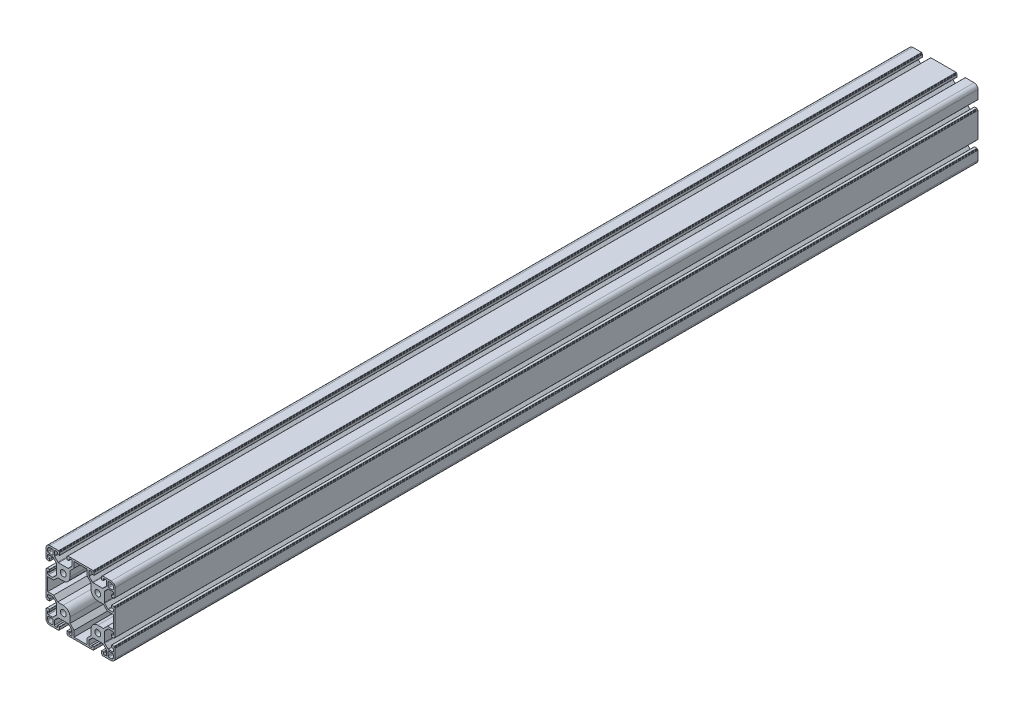
SolidWorks part; units mm, degrees
material "6063 T5"
ref_plane "Спереди" through (0, 0, 0) normal (0, 0, 1) x (1, 0, 0)
ref_plane "Сверху" through (0, 0, 0) normal (0, 1, 0) x (1, 0, 0)
ref_plane "Справа" through (0, 0, 0) normal (1, 0, 0) x (0, 0, -1)
sketch "Эскиз1" plane through (0, 0, 0) normal (0, 0, 1) x (1, 0, 0)
  line L0 (-19.98, 20.5457) -> (20.02, 20.5457) construction
  line L1 (-20, 10.25) -> (-20, 15.5)
  line L2 (-15.5, 20) -> (-10.25, 20)
  line L3 (20, 0) -> (20, -40) construction
  line L4 (-12.8, 11.8) -> (-17, 11.8)
  line L5 (-11.8, 12.8) -> (-11.8, 17)
  line L6 (-12.8, 18) -> (-15.5, 18)
  line L7 (-18, 12.8) -> (-18, 15.5)
  line L8 (0, 0) -> (40, 0) construction
  line L13 (0, 0) -> (0, -40) construction
  line L14 (0, -40) -> (40, -40) construction
  line L19 (40, 0) -> (40, -40) construction
  line L20 (50.25, 20) -> (55.5, 20)
  line L25 (0, -20) -> (40, -20) construction
  line L26 (60, 15.5) -> (60, 10.25)
  line L27 (51.8, 12.8) -> (51.8, 17)
  line L28 (52.8, 11.8) -> (57, 11.8)
  line L29 (58, 12.8) -> (58, 15.5)
  line L30 (52.8, 18) -> (55.5, 18)
  line L31 (60, -50.25) -> (60, -55.5)
  line L32 (55.5, -60) -> (50.25, -60)
  line L33 (52.8, -51.8) -> (57, -51.8)
  line L34 (51.8, -52.8) -> (51.8, -57)
  line L35 (52.8, -58) -> (55.5, -58)
  line L36 (58, -52.8) -> (58, -55.5)
  line L37 (-10.25, -60) -> (-15.5, -60)
  line L38 (-20, -55.5) -> (-20, -50.25)
  line L39 (-11.8, -52.8) -> (-11.8, -57)
  line L40 (-12.8, -51.8) -> (-17, -51.8)
  line L41 (-18, -52.8) -> (-18, -55.5)
  line L42 (-12.8, -58) -> (-15.5, -58)
  line L43 (10.25, 20) -> (29.75, 20)
  line L44 (60, -10.25) -> (60, -29.75)
  line L45 (29.75, -60) -> (10.25, -60)
  line L46 (-20, -29.75) -> (-20, -10.25)
  line L47 (-20.044, 23.5406) -> (59.956, 23.5406) construction
  line L48 (-18, -27.55) -> (-18, -12.45)
  line L49 (-18, -12.45) -> (-11.1387, -12.45)
  line L50 (-11.1387, -12.45) -> (-6.4887, -7.8)
  line L51 (-6.4887, -7.8) -> (0, -7.8)
  line L52 (7.8, 0) -> (7.8, 6.4887)
  line L53 (7.8, 6.4887) -> (12.45, 11.1387)
  line L54 (12.45, 11.1387) -> (12.45, 18)
  line L55 (12.45, 18) -> (27.55, 18)
  line L56 (12.45, -58) -> (27.55, -58)
  line L57 (12.45, -51.1387) -> (12.45, -58)
  line L58 (7.8, -46.4887) -> (12.45, -51.1387)
  line L59 (7.8, -40) -> (7.8, -46.4887)
  line L60 (-6.4887, -32.2) -> (0, -32.2)
  line L61 (-11.1387, -27.55) -> (-6.4887, -32.2)
  line L62 (-18, -27.55) -> (-11.1387, -27.55)
  line L63 (27.55, -51.1387) -> (27.55, -58)
  line L64 (32.2, -46.4887) -> (27.55, -51.1387)
  line L65 (32.2, -40) -> (32.2, -46.4887)
  line L66 (46.4887, -32.2) -> (40, -32.2)
  line L67 (51.1387, -27.55) -> (46.4887, -32.2)
  line L68 (58, -27.55) -> (51.1387, -27.55)
  line L69 (58, -27.55) -> (58, -12.45)
  line L70 (58, -12.45) -> (51.1387, -12.45)
  line L71 (51.1387, -12.45) -> (46.4887, -7.8)
  line L72 (46.4887, -7.8) -> (40, -7.8)
  line L73 (32.2, 0) -> (32.2, 6.4887)
  line L74 (32.2, 6.4887) -> (27.55, 11.1387)
  line L75 (27.55, 11.1387) -> (27.55, 18)
  arc A0 (-20, 15.5) -> (-15.5, 20) centre (-15.5, 15.5) cw
  arc A1 (-15.5, 18) -> (-18, 15.5) centre (-15.5, 15.5) ccw
  arc A2 (-17, 11.8) -> (-18, 12.8) centre (-17, 12.8) cw
  arc A3 (-12.8, 11.8) -> (-11.8, 12.8) centre (-12.8, 12.8) ccw
  arc A4 (-11.8, 17) -> (-12.8, 18) centre (-12.8, 17) ccw
  circle A5 centre (0, 0) radius 3.4
  arc A6 (55.5, 20) -> (60, 15.5) centre (55.5, 15.5) cw
  arc A11 (58, 15.5) -> (55.5, 18) centre (55.5, 15.5) ccw
  arc A16 (51.8, 17) -> (52.8, 18) centre (52.8, 17) cw
  arc A21 (51.8, 12.8) -> (52.8, 11.8) centre (52.8, 12.8) ccw
  arc A22 (57, 11.8) -> (58, 12.8) centre (57, 12.8) ccw
  circle A23 centre (40, 0) radius 3.4
  arc A24 (60, -55.5) -> (55.5, -60) centre (55.5, -55.5) cw
  arc A25 (55.5, -58) -> (58, -55.5) centre (55.5, -55.5) ccw
  arc A26 (57, -51.8) -> (58, -52.8) centre (57, -52.8) cw
  arc A27 (52.8, -51.8) -> (51.8, -52.8) centre (52.8, -52.8) ccw
  arc A28 (51.8, -57) -> (52.8, -58) centre (52.8, -57) ccw
  circle A29 centre (40, -40) radius 3.4
  arc A30 (-15.5, -60) -> (-20, -55.5) centre (-15.5, -55.5) cw
  arc A31 (-18, -55.5) -> (-15.5, -58) centre (-15.5, -55.5) ccw
  arc A32 (-11.8, -57) -> (-12.8, -58) centre (-12.8, -57) cw
  arc A33 (-11.8, -52.8) -> (-12.8, -51.8) centre (-12.8, -52.8) ccw
  arc A34 (-17, -51.8) -> (-18, -52.8) centre (-17, -52.8) ccw
  circle A35 centre (0, -40) radius 3.4
  arc A36 (0, -7.8) -> (7.8, 0) centre (0, 0) ccw
  arc A37 (0, -32.2) -> (7.8, -40) centre (0, -40) cw
  arc A38 (40, -32.2) -> (32.2, -40) centre (40, -40) ccw
  arc A39 (40, -7.8) -> (32.2, 0) centre (40, 0) cw
  point P5 (0, 0)
  point P27 (20, -20)
  point P36 (40, 0)
  point P57 (40, -40)
  point P77 (0, -40)
  point P94 (20, -20)
  point P122 (-18, -20)
  point P127 (20, -58)
  point P138 (20, 18)
  line B0 (-20, 10.25) -> (-20, 5.4)
  line B1 (-19.7, 5.1) -> (-19.3, 5.1)
  line B2 (-19, 4.8) -> (-19, 4.4)
  line B3 (-18.7, 4.1) -> (-16, 4.1)
  line B4 (-15.7, 4.4) -> (-15.7, 6.3)
  line B5 (-16, 6.6) -> (-17.2, 6.6)
  line B6 (-18.2, 7.6) -> (-18.2, 9.25)
  line B7 (-17.2, 10.25) -> (-12.4642, 10.25)
  line B8 (-11.7571, 9.9571) -> (-7.9929, 6.1929)
  line B9 (-7.7, 5.4858) -> (-7.7, -5.4858)
  line B10 (-7.7, 0) -> (-20, 0) construction
  line B11 (-11.7571, -9.9571) -> (-7.9929, -6.1929)
  line B12 (-17.2, -10.25) -> (-12.4642, -10.25)
  line B13 (-18.2, -7.6) -> (-18.2, -9.25)
  line B14 (-16, -6.6) -> (-17.2, -6.6)
  line B15 (-15.7, -4.4) -> (-15.7, -6.3)
  line B16 (-18.7, -4.1) -> (-16, -4.1)
  line B17 (-19, -4.8) -> (-19, -4.4)
  line B18 (-19.7, -5.1) -> (-19.3, -5.1)
  line B19 (-20, -10.25) -> (-20, -5.4)
  arc B20 (-15.7, 6.3) -> (-16, 6.6) centre (-16, 6.3) ccw
  arc B21 (-16, 4.1) -> (-15.7, 4.4) centre (-16, 4.4) ccw
  arc B22 (-19, 4.4) -> (-18.7, 4.1) centre (-18.7, 4.4) ccw
  arc B23 (-19.3, 5.1) -> (-19, 4.8) centre (-19.3, 4.8) cw
  arc B24 (-20, 5.4) -> (-19.7, 5.1) centre (-19.7, 5.4) ccw
  arc B25 (-7.9929, 6.1929) -> (-7.7, 5.4858) centre (-8.7, 5.4858) cw
  arc B26 (-12.4642, 10.25) -> (-11.7571, 9.9571) centre (-12.4642, 9.25) cw
  arc B27 (-18.2, 9.25) -> (-17.2, 10.25) centre (-17.2, 9.25) cw
  arc B28 (-17.2, 6.6) -> (-18.2, 7.6) centre (-17.2, 7.6) cw
  arc B29 (-17.2, -6.6) -> (-18.2, -7.6) centre (-17.2, -7.6) ccw
  arc B30 (-18.2, -9.25) -> (-17.2, -10.25) centre (-17.2, -9.25) ccw
  arc B31 (-12.4642, -10.25) -> (-11.7571, -9.9571) centre (-12.4642, -9.25) ccw
  arc B32 (-7.9929, -6.1929) -> (-7.7, -5.4858) centre (-8.7, -5.4858) ccw
  arc B33 (-20, -5.4) -> (-19.7, -5.1) centre (-19.7, -5.4) cw
  arc B34 (-19.3, -5.1) -> (-19, -4.8) centre (-19.3, -4.8) ccw
  arc B35 (-19, -4.4) -> (-18.7, -4.1) centre (-18.7, -4.4) cw
  arc B36 (-16, -4.1) -> (-15.7, -4.4) centre (-16, -4.4) cw
  arc B37 (-15.7, -6.3) -> (-16, -6.6) centre (-16, -6.3) cw
  line B38 (10.25, 20) -> (5.4, 20)
  line B39 (5.1, 19.7) -> (5.1, 19.3)
  line B40 (4.8, 19) -> (4.4, 19)
  line B41 (4.1, 18.7) -> (4.1, 16)
  line B42 (4.4, 15.7) -> (6.3, 15.7)
  line B43 (6.6, 16) -> (6.6, 17.2)
  line B44 (7.6, 18.2) -> (9.25, 18.2)
  line B45 (10.25, 17.2) -> (10.25, 12.4642)
  line B46 (9.9571, 11.7571) -> (6.1929, 7.9929)
  line B47 (5.4858, 7.7) -> (-5.4858, 7.7)
  line B48 (0, 7.7) -> (0, 20) construction
  line B49 (-9.9571, 11.7571) -> (-6.1929, 7.9929)
  line B50 (-10.25, 17.2) -> (-10.25, 12.4642)
  line B51 (-7.6, 18.2) -> (-9.25, 18.2)
  line B52 (-6.6, 16) -> (-6.6, 17.2)
  line B53 (-4.4, 15.7) -> (-6.3, 15.7)
  line B54 (-4.1, 18.7) -> (-4.1, 16)
  line B55 (-4.8, 19) -> (-4.4, 19)
  line B56 (-5.1, 19.7) -> (-5.1, 19.3)
  line B57 (-10.25, 20) -> (-5.4, 20)
  arc B58 (6.3, 15.7) -> (6.6, 16) centre (6.3, 16) ccw
  arc B59 (4.1, 16) -> (4.4, 15.7) centre (4.4, 16) ccw
  arc B60 (4.4, 19) -> (4.1, 18.7) centre (4.4, 18.7) ccw
  arc B61 (5.1, 19.3) -> (4.8, 19) centre (4.8, 19.3) cw
  arc B62 (5.4, 20) -> (5.1, 19.7) centre (5.4, 19.7) ccw
  arc B63 (6.1929, 7.9929) -> (5.4858, 7.7) centre (5.4858, 8.7) cw
  arc B64 (10.25, 12.4642) -> (9.9571, 11.7571) centre (9.25, 12.4642) cw
  arc B65 (9.25, 18.2) -> (10.25, 17.2) centre (9.25, 17.2) cw
  arc B66 (6.6, 17.2) -> (7.6, 18.2) centre (7.6, 17.2) cw
  arc B67 (-6.6, 17.2) -> (-7.6, 18.2) centre (-7.6, 17.2) ccw
  arc B68 (-9.25, 18.2) -> (-10.25, 17.2) centre (-9.25, 17.2) ccw
  arc B69 (-10.25, 12.4642) -> (-9.9571, 11.7571) centre (-9.25, 12.4642) ccw
  arc B70 (-6.1929, 7.9929) -> (-5.4858, 7.7) centre (-5.4858, 8.7) ccw
  arc B71 (-5.4, 20) -> (-5.1, 19.7) centre (-5.4, 19.7) cw
  arc B72 (-5.1, 19.3) -> (-4.8, 19) centre (-4.8, 19.3) ccw
  arc B73 (-4.4, 19) -> (-4.1, 18.7) centre (-4.4, 18.7) cw
  arc B74 (-4.1, 16) -> (-4.4, 15.7) centre (-4.4, 16) cw
  arc B75 (-6.3, 15.7) -> (-6.6, 16) centre (-6.3, 16) cw
  line B76 (50.25, 20) -> (45.4, 20)
  line B77 (45.1, 19.7) -> (45.1, 19.3)
  line B78 (44.8, 19) -> (44.4, 19)
  line B79 (44.1, 18.7) -> (44.1, 16)
  line B80 (44.4, 15.7) -> (46.3, 15.7)
  line B81 (46.6, 16) -> (46.6, 17.2)
  line B82 (47.6, 18.2) -> (49.25, 18.2)
  line B83 (50.25, 17.2) -> (50.25, 12.4642)
  line B84 (49.9571, 11.7571) -> (46.1929, 7.9929)
  line B85 (45.4858, 7.7) -> (34.5142, 7.7)
  line B86 (40, 7.7) -> (40, 20) construction
  line B87 (30.0429, 11.7571) -> (33.8071, 7.9929)
  line B88 (29.75, 17.2) -> (29.75, 12.4642)
  line B89 (32.4, 18.2) -> (30.75, 18.2)
  line B90 (33.4, 16) -> (33.4, 17.2)
  line B91 (35.6, 15.7) -> (33.7, 15.7)
  line B92 (35.9, 18.7) -> (35.9, 16)
  line B93 (35.2, 19) -> (35.6, 19)
  line B94 (34.9, 19.7) -> (34.9, 19.3)
  line B95 (29.75, 20) -> (34.6, 20)
  arc B96 (46.3, 15.7) -> (46.6, 16) centre (46.3, 16) ccw
  arc B97 (44.1, 16) -> (44.4, 15.7) centre (44.4, 16) ccw
  arc B98 (44.4, 19) -> (44.1, 18.7) centre (44.4, 18.7) ccw
  arc B99 (45.1, 19.3) -> (44.8, 19) centre (44.8, 19.3) cw
  arc B100 (45.4, 20) -> (45.1, 19.7) centre (45.4, 19.7) ccw
  arc B101 (46.1929, 7.9929) -> (45.4858, 7.7) centre (45.4858, 8.7) cw
  arc B102 (50.25, 12.4642) -> (49.9571, 11.7571) centre (49.25, 12.4642) cw
  arc B103 (49.25, 18.2) -> (50.25, 17.2) centre (49.25, 17.2) cw
  arc B104 (46.6, 17.2) -> (47.6, 18.2) centre (47.6, 17.2) cw
  arc B105 (33.4, 17.2) -> (32.4, 18.2) centre (32.4, 17.2) ccw
  arc B106 (30.75, 18.2) -> (29.75, 17.2) centre (30.75, 17.2) ccw
  arc B107 (29.75, 12.4642) -> (30.0429, 11.7571) centre (30.75, 12.4642) ccw
  arc B108 (33.8071, 7.9929) -> (34.5142, 7.7) centre (34.5142, 8.7) ccw
  arc B109 (34.6, 20) -> (34.9, 19.7) centre (34.6, 19.7) cw
  arc B110 (34.9, 19.3) -> (35.2, 19) centre (35.2, 19.3) ccw
  arc B111 (35.6, 19) -> (35.9, 18.7) centre (35.6, 18.7) cw
  arc B112 (35.9, 16) -> (35.6, 15.7) centre (35.6, 16) cw
  arc B113 (33.7, 15.7) -> (33.4, 16) centre (33.7, 16) cw
  line B114 (60, -10.25) -> (60, -5.4)
  line B115 (59.7, -5.1) -> (59.3, -5.1)
  line B116 (59, -4.8) -> (59, -4.4)
  line B117 (58.7, -4.1) -> (56, -4.1)
  line B118 (55.7, -4.4) -> (55.7, -6.3)
  line B119 (56, -6.6) -> (57.2, -6.6)
  line B120 (58.2, -7.6) -> (58.2, -9.25)
  line B121 (57.2, -10.25) -> (52.4642, -10.25)
  line B122 (51.7571, -9.9571) -> (47.9929, -6.1929)
  line B123 (47.7, -5.4858) -> (47.7, 5.4858)
  line B124 (47.7, 0) -> (60, 0) construction
  line B125 (51.7571, 9.9571) -> (47.9929, 6.1929)
  line B126 (57.2, 10.25) -> (52.4642, 10.25)
  line B127 (58.2, 7.6) -> (58.2, 9.25)
  line B128 (56, 6.6) -> (57.2, 6.6)
  line B129 (55.7, 4.4) -> (55.7, 6.3)
  line B130 (58.7, 4.1) -> (56, 4.1)
  line B131 (59, 4.8) -> (59, 4.4)
  line B132 (59.7, 5.1) -> (59.3, 5.1)
  line B133 (60, 10.25) -> (60, 5.4)
  arc B134 (55.7, -6.3) -> (56, -6.6) centre (56, -6.3) ccw
  arc B135 (56, -4.1) -> (55.7, -4.4) centre (56, -4.4) ccw
  arc B136 (59, -4.4) -> (58.7, -4.1) centre (58.7, -4.4) ccw
  arc B137 (59.3, -5.1) -> (59, -4.8) centre (59.3, -4.8) cw
  arc B138 (60, -5.4) -> (59.7, -5.1) centre (59.7, -5.4) ccw
  arc B139 (47.9929, -6.1929) -> (47.7, -5.4858) centre (48.7, -5.4858) cw
  arc B140 (52.4642, -10.25) -> (51.7571, -9.9571) centre (52.4642, -9.25) cw
  arc B141 (58.2, -9.25) -> (57.2, -10.25) centre (57.2, -9.25) cw
  arc B142 (57.2, -6.6) -> (58.2, -7.6) centre (57.2, -7.6) cw
  arc B143 (57.2, 6.6) -> (58.2, 7.6) centre (57.2, 7.6) ccw
  arc B144 (58.2, 9.25) -> (57.2, 10.25) centre (57.2, 9.25) ccw
  arc B145 (52.4642, 10.25) -> (51.7571, 9.9571) centre (52.4642, 9.25) ccw
  arc B146 (47.9929, 6.1929) -> (47.7, 5.4858) centre (48.7, 5.4858) ccw
  arc B147 (60, 5.4) -> (59.7, 5.1) centre (59.7, 5.4) cw
  arc B148 (59.3, 5.1) -> (59, 4.8) centre (59.3, 4.8) ccw
  arc B149 (59, 4.4) -> (58.7, 4.1) centre (58.7, 4.4) cw
  arc B150 (56, 4.1) -> (55.7, 4.4) centre (56, 4.4) cw
  arc B151 (55.7, 6.3) -> (56, 6.6) centre (56, 6.3) cw
  line B152 (60, -50.25) -> (60, -45.4)
  line B153 (59.7, -45.1) -> (59.3, -45.1)
  line B154 (59, -44.8) -> (59, -44.4)
  line B155 (58.7, -44.1) -> (56, -44.1)
  line B156 (55.7, -44.4) -> (55.7, -46.3)
  line B157 (56, -46.6) -> (57.2, -46.6)
  line B158 (58.2, -47.6) -> (58.2, -49.25)
  line B159 (57.2, -50.25) -> (52.4642, -50.25)
  line B160 (51.7571, -49.9571) -> (47.9929, -46.1929)
  line B161 (47.7, -45.4858) -> (47.7, -34.5142)
  line B162 (47.7, -40) -> (60, -40) construction
  line B163 (51.7571, -30.0429) -> (47.9929, -33.8071)
  line B164 (57.2, -29.75) -> (52.4642, -29.75)
  line B165 (58.2, -32.4) -> (58.2, -30.75)
  line B166 (56, -33.4) -> (57.2, -33.4)
  line B167 (55.7, -35.6) -> (55.7, -33.7)
  line B168 (58.7, -35.9) -> (56, -35.9)
  line B169 (59, -35.2) -> (59, -35.6)
  line B170 (59.7, -34.9) -> (59.3, -34.9)
  line B171 (60, -29.75) -> (60, -34.6)
  arc B172 (55.7, -46.3) -> (56, -46.6) centre (56, -46.3) ccw
  arc B173 (56, -44.1) -> (55.7, -44.4) centre (56, -44.4) ccw
  arc B174 (59, -44.4) -> (58.7, -44.1) centre (58.7, -44.4) ccw
  arc B175 (59.3, -45.1) -> (59, -44.8) centre (59.3, -44.8) cw
  arc B176 (60, -45.4) -> (59.7, -45.1) centre (59.7, -45.4) ccw
  arc B177 (47.9929, -46.1929) -> (47.7, -45.4858) centre (48.7, -45.4858) cw
  arc B178 (52.4642, -50.25) -> (51.7571, -49.9571) centre (52.4642, -49.25) cw
  arc B179 (58.2, -49.25) -> (57.2, -50.25) centre (57.2, -49.25) cw
  arc B180 (57.2, -46.6) -> (58.2, -47.6) centre (57.2, -47.6) cw
  arc B181 (57.2, -33.4) -> (58.2, -32.4) centre (57.2, -32.4) ccw
  arc B182 (58.2, -30.75) -> (57.2, -29.75) centre (57.2, -30.75) ccw
  arc B183 (52.4642, -29.75) -> (51.7571, -30.0429) centre (52.4642, -30.75) ccw
  arc B184 (47.9929, -33.8071) -> (47.7, -34.5142) centre (48.7, -34.5142) ccw
  arc B185 (60, -34.6) -> (59.7, -34.9) centre (59.7, -34.6) cw
  arc B186 (59.3, -34.9) -> (59, -35.2) centre (59.3, -35.2) ccw
  arc B187 (59, -35.6) -> (58.7, -35.9) centre (58.7, -35.6) cw
  arc B188 (56, -35.9) -> (55.7, -35.6) centre (56, -35.6) cw
  arc B189 (55.7, -33.7) -> (56, -33.4) centre (56, -33.7) cw
  line B190 (29.75, -60) -> (34.6, -60)
  line B191 (34.9, -59.7) -> (34.9, -59.3)
  line B192 (35.2, -59) -> (35.6, -59)
  line B193 (35.9, -58.7) -> (35.9, -56)
  line B194 (35.6, -55.7) -> (33.7, -55.7)
  line B195 (33.4, -56) -> (33.4, -57.2)
  line B196 (32.4, -58.2) -> (30.75, -58.2)
  line B197 (29.75, -57.2) -> (29.75, -52.4642)
  line B198 (30.0429, -51.7571) -> (33.8071, -47.9929)
  line B199 (34.5142, -47.7) -> (45.4858, -47.7)
  line B200 (40, -47.7) -> (40, -60) construction
  line B201 (49.9571, -51.7571) -> (46.1929, -47.9929)
  line B202 (50.25, -57.2) -> (50.25, -52.4642)
  line B203 (47.6, -58.2) -> (49.25, -58.2)
  line B204 (46.6, -56) -> (46.6, -57.2)
  line B205 (44.4, -55.7) -> (46.3, -55.7)
  line B206 (44.1, -58.7) -> (44.1, -56)
  line B207 (44.8, -59) -> (44.4, -59)
  line B208 (45.1, -59.7) -> (45.1, -59.3)
  line B209 (50.25, -60) -> (45.4, -60)
  arc B210 (33.7, -55.7) -> (33.4, -56) centre (33.7, -56) ccw
  arc B211 (35.9, -56) -> (35.6, -55.7) centre (35.6, -56) ccw
  arc B212 (35.6, -59) -> (35.9, -58.7) centre (35.6, -58.7) ccw
  arc B213 (34.9, -59.3) -> (35.2, -59) centre (35.2, -59.3) cw
  arc B214 (34.6, -60) -> (34.9, -59.7) centre (34.6, -59.7) ccw
  arc B215 (33.8071, -47.9929) -> (34.5142, -47.7) centre (34.5142, -48.7) cw
  arc B216 (29.75, -52.4642) -> (30.0429, -51.7571) centre (30.75, -52.4642) cw
  arc B217 (30.75, -58.2) -> (29.75, -57.2) centre (30.75, -57.2) cw
  arc B218 (33.4, -57.2) -> (32.4, -58.2) centre (32.4, -57.2) cw
  arc B219 (46.6, -57.2) -> (47.6, -58.2) centre (47.6, -57.2) ccw
  arc B220 (49.25, -58.2) -> (50.25, -57.2) centre (49.25, -57.2) ccw
  arc B221 (50.25, -52.4642) -> (49.9571, -51.7571) centre (49.25, -52.4642) ccw
  arc B222 (46.1929, -47.9929) -> (45.4858, -47.7) centre (45.4858, -48.7) ccw
  arc B223 (45.4, -60) -> (45.1, -59.7) centre (45.4, -59.7) cw
  arc B224 (45.1, -59.3) -> (44.8, -59) centre (44.8, -59.3) ccw
  arc B225 (44.4, -59) -> (44.1, -58.7) centre (44.4, -58.7) cw
  arc B226 (44.1, -56) -> (44.4, -55.7) centre (44.4, -56) cw
  arc B227 (46.3, -55.7) -> (46.6, -56) centre (46.3, -56) cw
  line B228 (-10.25, -60) -> (-5.4, -60)
  line B229 (-5.1, -59.7) -> (-5.1, -59.3)
  line B230 (-4.8, -59) -> (-4.4, -59)
  line B231 (-4.1, -58.7) -> (-4.1, -56)
  line B232 (-4.4, -55.7) -> (-6.3, -55.7)
  line B233 (-6.6, -56) -> (-6.6, -57.2)
  line B234 (-7.6, -58.2) -> (-9.25, -58.2)
  line B235 (-10.25, -57.2) -> (-10.25, -52.4642)
  line B236 (-9.9571, -51.7571) -> (-6.1929, -47.9929)
  line B237 (-5.4858, -47.7) -> (5.4858, -47.7)
  line B238 (0, -47.7) -> (0, -60) construction
  line B239 (9.9571, -51.7571) -> (6.1929, -47.9929)
  line B240 (10.25, -57.2) -> (10.25, -52.4642)
  line B241 (7.6, -58.2) -> (9.25, -58.2)
  line B242 (6.6, -56) -> (6.6, -57.2)
  line B243 (4.4, -55.7) -> (6.3, -55.7)
  line B244 (4.1, -58.7) -> (4.1, -56)
  line B245 (4.8, -59) -> (4.4, -59)
  line B246 (5.1, -59.7) -> (5.1, -59.3)
  line B247 (10.25, -60) -> (5.4, -60)
  arc B248 (-6.3, -55.7) -> (-6.6, -56) centre (-6.3, -56) ccw
  arc B249 (-4.1, -56) -> (-4.4, -55.7) centre (-4.4, -56) ccw
  arc B250 (-4.4, -59) -> (-4.1, -58.7) centre (-4.4, -58.7) ccw
  arc B251 (-5.1, -59.3) -> (-4.8, -59) centre (-4.8, -59.3) cw
  arc B252 (-5.4, -60) -> (-5.1, -59.7) centre (-5.4, -59.7) ccw
  arc B253 (-6.1929, -47.9929) -> (-5.4858, -47.7) centre (-5.4858, -48.7) cw
  arc B254 (-10.25, -52.4642) -> (-9.9571, -51.7571) centre (-9.25, -52.4642) cw
  arc B255 (-9.25, -58.2) -> (-10.25, -57.2) centre (-9.25, -57.2) cw
  arc B256 (-6.6, -57.2) -> (-7.6, -58.2) centre (-7.6, -57.2) cw
  arc B257 (6.6, -57.2) -> (7.6, -58.2) centre (7.6, -57.2) ccw
  arc B258 (9.25, -58.2) -> (10.25, -57.2) centre (9.25, -57.2) ccw
  arc B259 (10.25, -52.4642) -> (9.9571, -51.7571) centre (9.25, -52.4642) ccw
  arc B260 (6.1929, -47.9929) -> (5.4858, -47.7) centre (5.4858, -48.7) ccw
  arc B261 (5.4, -60) -> (5.1, -59.7) centre (5.4, -59.7) cw
  arc B262 (5.1, -59.3) -> (4.8, -59) centre (4.8, -59.3) ccw
  arc B263 (4.4, -59) -> (4.1, -58.7) centre (4.4, -58.7) cw
  arc B264 (4.1, -56) -> (4.4, -55.7) centre (4.4, -56) cw
  arc B265 (6.3, -55.7) -> (6.6, -56) centre (6.3, -56) cw
  line B266 (-20, -29.75) -> (-20, -34.6)
  line B267 (-19.7, -34.9) -> (-19.3, -34.9)
  line B268 (-19, -35.2) -> (-19, -35.6)
  line B269 (-18.7, -35.9) -> (-16, -35.9)
  line B270 (-15.7, -35.6) -> (-15.7, -33.7)
  line B271 (-16, -33.4) -> (-17.2, -33.4)
  line B272 (-18.2, -32.4) -> (-18.2, -30.75)
  line B273 (-17.2, -29.75) -> (-12.4642, -29.75)
  line B274 (-11.7571, -30.0429) -> (-7.9929, -33.8071)
  line B275 (-7.7, -34.5142) -> (-7.7, -45.4858)
  line B276 (-7.7, -40) -> (-20, -40) construction
  line B277 (-11.7571, -49.9571) -> (-7.9929, -46.1929)
  line B278 (-17.2, -50.25) -> (-12.4642, -50.25)
  line B279 (-18.2, -47.6) -> (-18.2, -49.25)
  line B280 (-16, -46.6) -> (-17.2, -46.6)
  line B281 (-15.7, -44.4) -> (-15.7, -46.3)
  line B282 (-18.7, -44.1) -> (-16, -44.1)
  line B283 (-19, -44.8) -> (-19, -44.4)
  line B284 (-19.7, -45.1) -> (-19.3, -45.1)
  line B285 (-20, -50.25) -> (-20, -45.4)
  arc B286 (-15.7, -33.7) -> (-16, -33.4) centre (-16, -33.7) ccw
  arc B287 (-16, -35.9) -> (-15.7, -35.6) centre (-16, -35.6) ccw
  arc B288 (-19, -35.6) -> (-18.7, -35.9) centre (-18.7, -35.6) ccw
  arc B289 (-19.3, -34.9) -> (-19, -35.2) centre (-19.3, -35.2) cw
  arc B290 (-20, -34.6) -> (-19.7, -34.9) centre (-19.7, -34.6) ccw
  arc B291 (-7.9929, -33.8071) -> (-7.7, -34.5142) centre (-8.7, -34.5142) cw
  arc B292 (-12.4642, -29.75) -> (-11.7571, -30.0429) centre (-12.4642, -30.75) cw
  arc B293 (-18.2, -30.75) -> (-17.2, -29.75) centre (-17.2, -30.75) cw
  arc B294 (-17.2, -33.4) -> (-18.2, -32.4) centre (-17.2, -32.4) cw
  arc B295 (-17.2, -46.6) -> (-18.2, -47.6) centre (-17.2, -47.6) ccw
  arc B296 (-18.2, -49.25) -> (-17.2, -50.25) centre (-17.2, -49.25) ccw
  arc B297 (-12.4642, -50.25) -> (-11.7571, -49.9571) centre (-12.4642, -49.25) ccw
  arc B298 (-7.9929, -46.1929) -> (-7.7, -45.4858) centre (-8.7, -45.4858) ccw
  arc B299 (-20, -45.4) -> (-19.7, -45.1) centre (-19.7, -45.4) cw
  arc B300 (-19.3, -45.1) -> (-19, -44.8) centre (-19.3, -44.8) ccw
  arc B301 (-19, -44.4) -> (-18.7, -44.1) centre (-18.7, -44.4) cw
  arc B302 (-16, -44.1) -> (-15.7, -44.4) centre (-16, -44.4) cw
  arc B303 (-15.7, -46.3) -> (-16, -46.6) centre (-16, -46.3) cw
  dimension "D12" = 7.8
  dimension "D2" = 4.5
  dimension "D3" = 2.5
  dimension "D5" = 1
  dimension "D6" = 6.8
  dimension "D1" = 20
  dimension "D4" = 6.2
  dimension "D7" = 40
  dimension "D8" = 80
  dimension "D9" = 2.2
  dimension "D10" = 2.2
  dimension "D11" = 4
sketch_block_instance "8B(20,5PL)-1"
sketch_block "8B(20,5PL)" parameters "D7"=0.3, "D8"=1, "D1"=12.3, "D2"=4.3, "D3"=8.2, "D4"=20.5, "D5"=10.2, "D6"=135
sketch_block_instance "8B(20,5PL)-3"
sketch_block_instance "8B(20,5PL)-6"
sketch_block_instance "8B(20,5PL)-7"
sketch_block_instance "8B(20,5PL)-8"
sketch_block_instance "8B(20,5PL)-9"
sketch_block_instance "8B(20,5PL)-10"
sketch_block_instance "8B(20,5PL)-11"
sketch_block_instance "8B(20,5PL)-12"
sketch_block_instance "8B(20,5PL)-13"
extrude "Бобышка-Вытянуть1" add sketch "Эскиз1" along normal blind 1000
